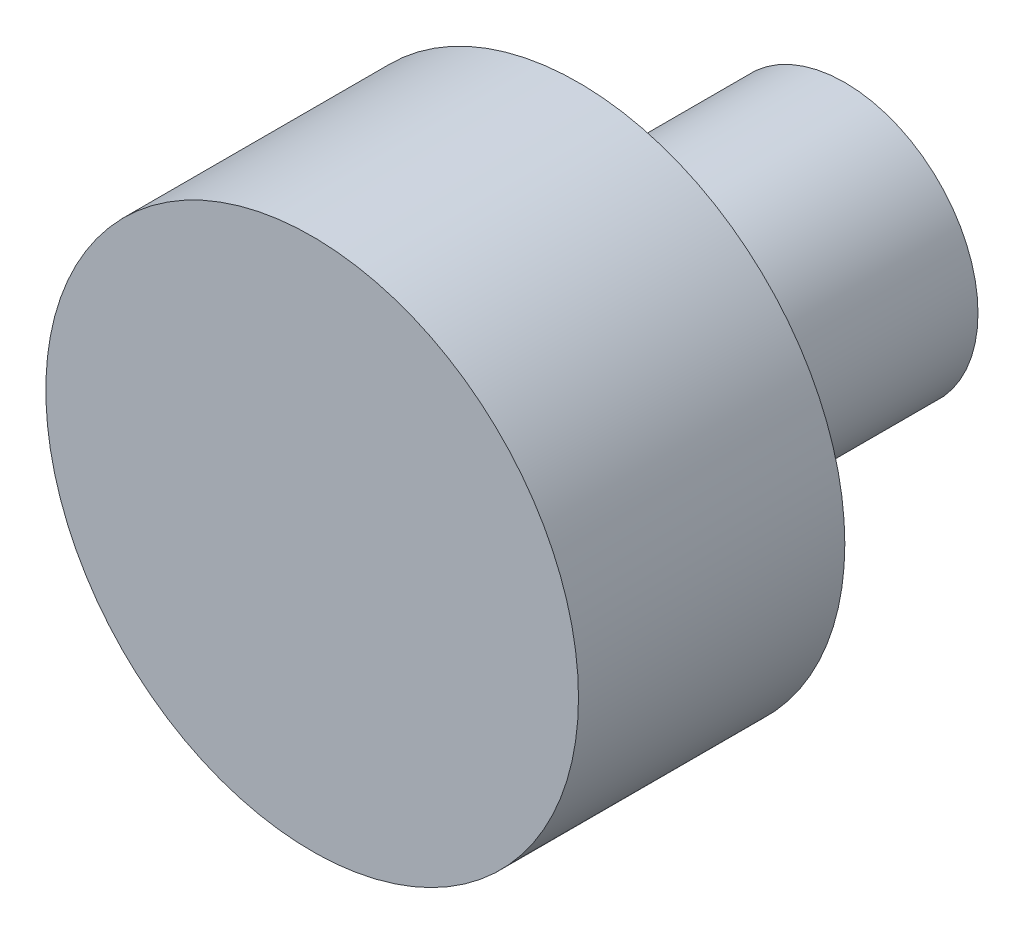
SolidWorks part; units mm, degrees
ref_plane "Front Plane" through (0, 0, 0) normal (0, 0, 1) x (1, 0, 0)
ref_plane "Top Plane" through (0, 0, 0) normal (0, 1, 0) x (1, 0, 0)
ref_plane "Right Plane" through (0, 0, 0) normal (1, 0, 0) x (0, 0, -1)
sketch "Sketch1" plane through (0, 0, 0) normal (0, 0, 1) x (1, 0, 0)
  circle A0 centre (0, 0) radius 10
  dimension "D1" = 20
extrude "Boss-Extrude1" add sketch "Sketch1" along normal blind 20
sketch "Sketch2" plane through (0, 0, 0) normal (0, 0, -1) x (-1, 0, 0)
  circle A0 centre (0, 0) radius 5
  dimension "D1" = 10
extrude "Boss-Extrude2" add sketch "Sketch2" along normal blind 10
sketch "Sketch3" plane through (0, 0, 20) normal (0, 0, 1) x (1, 0, 0)
  circle A0 centre (0, 0) radius 10
extrude "Cut-Extrude1" cut sketch "Sketch3" against normal blind 10
